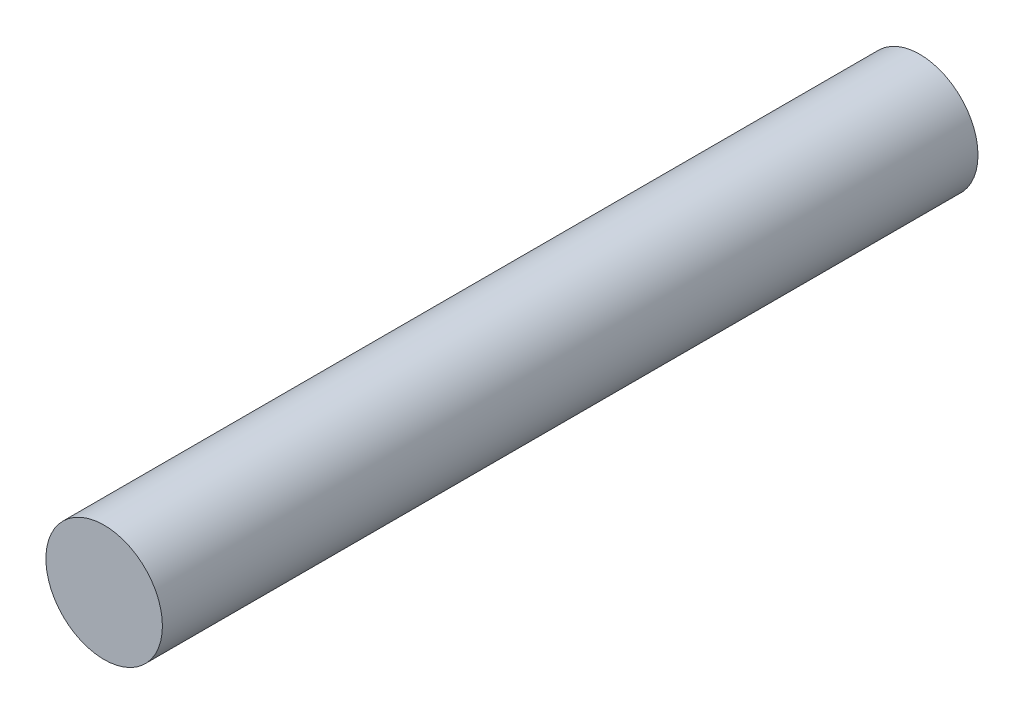
SolidWorks part; units mm, degrees
ref_plane "Alzado" through (0, 0, 0) normal (0, 0, 1) x (1, 0, 0)
ref_plane "Planta" through (0, 0, 0) normal (0, 1, 0) x (1, 0, 0)
ref_plane "Vista lateral" through (0, 0, 0) normal (1, 0, 0) x (0, 0, -1)
sketch "Croquis1" plane through (0, 0, 0) normal (0, 0, 1) x (1, 0, 0)
  circle A0 centre (0, 0) radius 6.35
  dimension "D1" = 12.7
extrude "Saliente-Extruir1" add sketch "Croquis1" along normal blind 88.9
